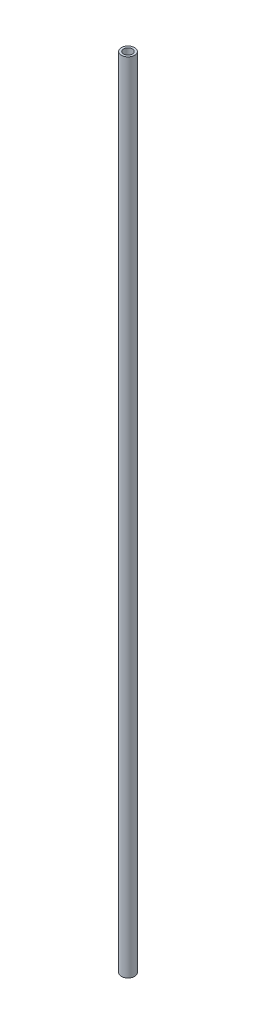
SolidWorks part; units mm, degrees
ref_plane "Front Plane" through (0, 0, 0) normal (0, 0, 1) x (1, 0, 0)
ref_plane "Top Plane" through (0, 0, 0) normal (0, 1, 0) x (1, 0, 0)
ref_plane "Right Plane" through (0, 0, 0) normal (1, 0, 0) x (0, 0, -1)
sketch "Sketch1" plane through (0, 0, 0) normal (0, 1, 0) x (1, 0, 0)
  circle A0 centre (0, 0) radius 3
  circle A1 centre (0, 0) radius 2
  dimension "D1" = 4
  dimension "D2" = 6
extrude "Boss-Extrude1" add sketch "Sketch1" along normal blind 360.04
equation "\"ID\"=4"
equation "\"D1@Sketch1\"=\"ID\""
equation "\"OD\"=6"
equation "\"D2@Sketch1\"=\"OD\""
equation "\"D1@Boss-Extrude1\"= \"ActualRodLength\""
equation "\"TraxxasOffset\"= 17.09"
equation "\"DeltaRodLength\"= 394.22"
equation "\"ActualRodLength\"= \"DeltaRodLength\" - \"TraxxasOffset\" * 2"
